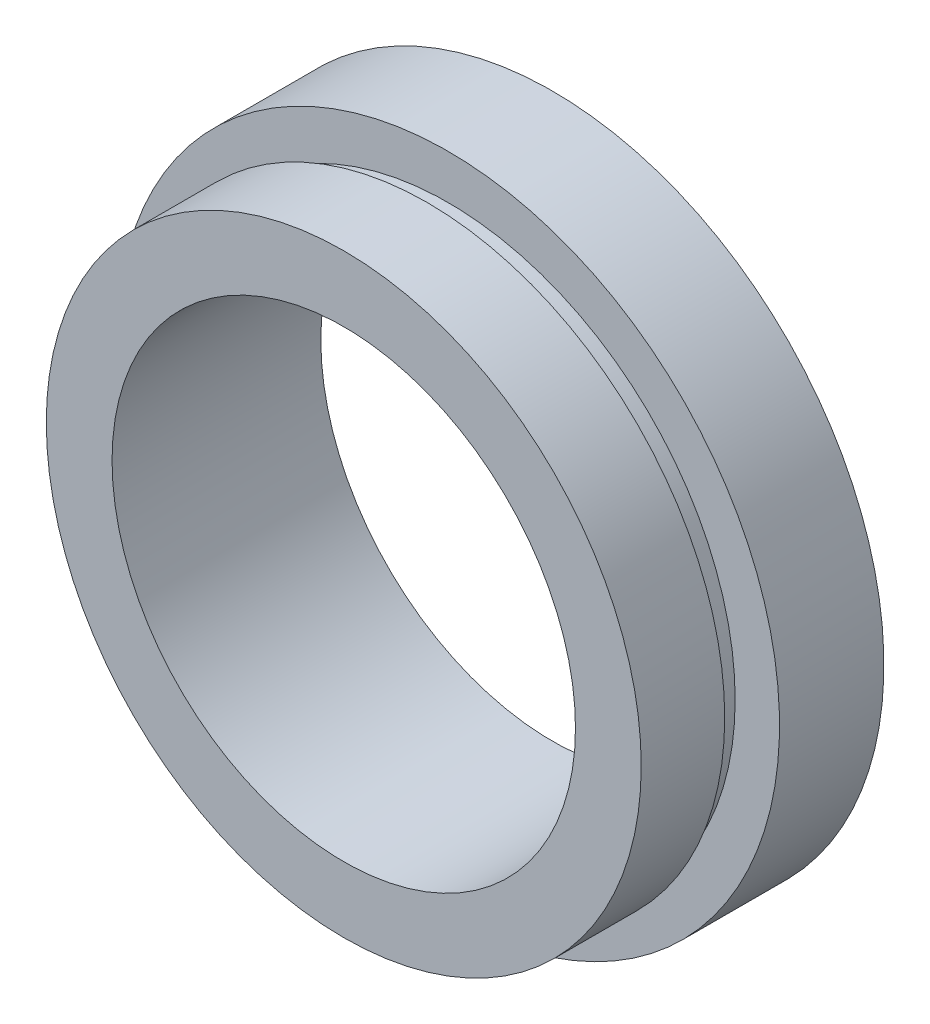
SolidWorks part; units mm, degrees
ref_plane "前视基准面" through (0, 0, 0) normal (0, 0, 1) x (1, 0, 0)
ref_plane "上视基准面" through (0, 0, 0) normal (0, 1, 0) x (1, 0, 0)
ref_plane "右视基准面" through (0, 0, 0) normal (1, 0, 0) x (0, 0, -1)
sketch "草图1" plane through (0, 0, 0) normal (0, 1, 0) x (1, 0, 0)
  line L0 (0, 19.1406) -> (0, -28.4043) construction
  line L1 (11.1, 0) -> (11.1, 10)
  line L2 (11.1, 0) -> (14.25, 0)
  line L3 (14.25, 0) -> (14.25, 4)
  line L4 (14.25, 4) -> (13.75, 4)
  line L5 (13.75, 4) -> (13.75, 5)
  line L6 (13.75, 5) -> (15.875, 5)
  line L7 (15.875, 5) -> (15.875, 10)
  line L8 (15.875, 10) -> (11.1, 10)
  dimension "D3" = 13.75
  dimension "D1" = 11.1
  dimension "D2" = 14.25
  dimension "D4" = 15.875
  dimension "D5" = 1
  dimension "D6" = 5
  dimension "D7" = 10
revolve "旋转1" add sketch "草图1" angle 360 about L0
cosmetic thread "装饰螺纹线1" parameters "D2"=23.2
cosmetic thread "装饰螺纹线2" parameters "D2"=27.5
